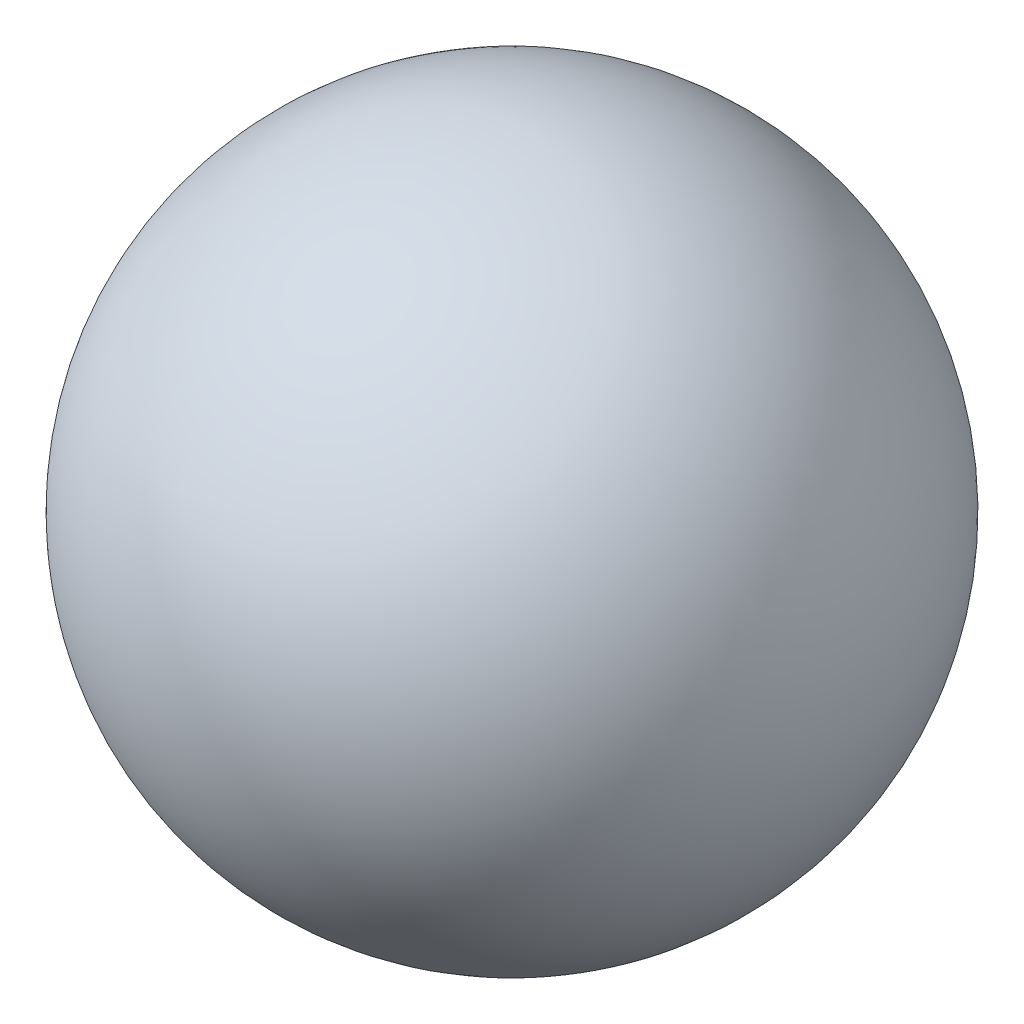
SolidWorks part; units mm, degrees
ref_plane "Front Plane" through (0, 0, 0) normal (0, 0, 1) x (1, 0, 0)
ref_plane "Top Plane" through (0, 0, 0) normal (0, 1, 0) x (1, 0, 0)
ref_plane "Right Plane" through (0, 0, 0) normal (1, 0, 0) x (0, 0, -1)
sketch "Sketch1" plane through (0, 0, 0) normal (0, 0, 1) x (1, 0, 0)
  line L0 (-15.5189, 87.535) -> (15.5189, -87.535)
  circle A0 centre (0, 0) radius 88.9
  dimension "D1" = 177.8
revolve "Revolve1" add sketch "Sketch1" angle 360 about L0
